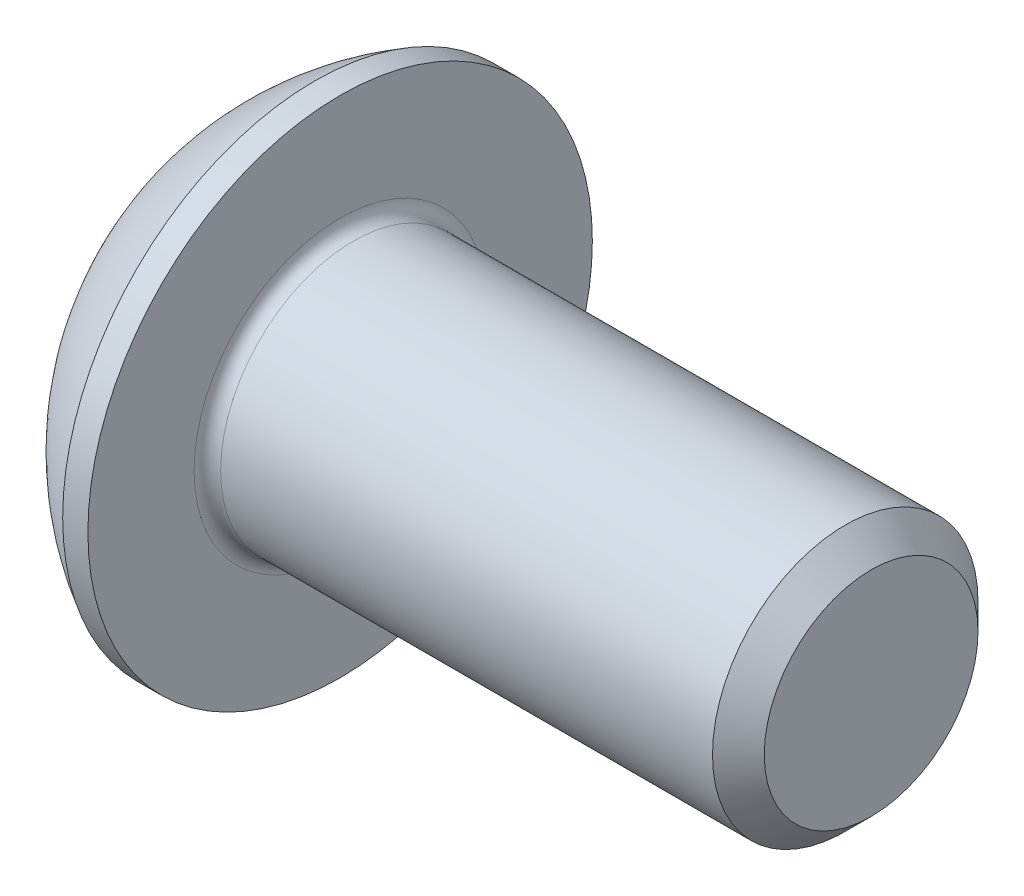
SolidWorks part; units mm, degrees
ref_plane "Plane1" through (0, 0, 0) normal (0, 0, 1) x (1, 0, 0)
ref_plane "Plane2" through (0, 0, 0) normal (0, 1, 0) x (1, 0, 0)
ref_plane "Plane3" through (0, 0, 0) normal (1, 0, 0) x (0, 0, -1)
sketch "BodySke" plane through (0, 0, 0) normal (0, 0, 1) x (1, 0, 0)
  line L0 (10.2, 0) -> (10.2, 1.61)
  line L1 (9.81, 2) -> (2.2, 2)
  line L2 (2.2, 2) -> (2.2, 3.8)
  line L3 (2.2, 3.8) -> (1.82, 3.8)
  line L4 (0, 0) -> (101.6, 0) construction
  line L5 (2.2, -3.8) -> (1.82, -3.8) construction
  line L6 (55.6768, -2) -> (2.2, -2) construction
  line L7 (10.2, 0) -> (0, 0)
  line L8 (0, 1.9) -> (0, -1.9) construction
  line L9 (0, 0) -> (0, 1.9)
  line L10 (10.2, 1.61) -> (9.81, 2)
  line L11 (10.2, -1.61) -> (9.81, -2) construction
  line L12 (2.9, 9.525) -> (2.9, -2) construction
  line L13 (2.2, 9.525) -> (2.2, -2) construction
  arc A1 (0, 1.9) -> (1.82, 3.8) centre (3.8853, 0) cw
  dimension "Diameter" = 4
  dimension "Length" = 8
  dimension "Head_dia" = 7.6
  dimension "D1" = 3.8
  dimension "Head_ht" = 2.2
  dimension "Head_side_ht" = 0.38
  dimension "Minor_dia" = 3.22
  dimension "Body_ch_ang" = 45
  dimension "Advance" = 0.7
  dimension "Thread_nom" = 8
revolve "BaseBody" add sketch "BodySke" angle 360 about L4
cosmetic thread "ThreadCosmetic" [suppressed] parameters "Thread_length"=6.6, "Thread_minor"=3.22
fillet "Fillet1" radius 0.2 1 edges at (2.2, 0, 2)
sketch "Sketch2" plane through (0, 0, 0) normal (0, 0, 1) x (1, 0, 0)
  line L0 (0, 1.25) -> (1.3, 1.25)
  line L1 (1.3, 1.25) -> (2.0217, 0)
  line L3 (2.0217, 0) -> (0, 0)
  line L4 (0, 0) -> (0, 1.25)
  line L5 (0, -1.25) -> (1.3, -1.25) construction
  line L6 (0, 0) -> (47.625, 0) construction
  dimension "D2" = 60
  dimension "PreBroach_depth" = 1.3
  dimension "PreBroach_dia" = 2.5
revolve "PreBroach" cut sketch "Sketch2" angle 360 about L6
sketch "Sketch3" plane through (0, 0, 0) normal (1, 0, 0) x (0, 0, -1)
  line L0 (-1.25, -0.7217) -> (-1.25, 0.7217)
  line L1 (-1.25, 0.7217) -> (0, 1.4434)
  line L2 (0, 1.4434) -> (1.25, 0.7217)
  line L3 (1.25, 0.7217) -> (1.25, -0.7217)
  line L4 (1.25, -0.7217) -> (0, -1.4434)
  line L5 (0, -1.4434) -> (-1.25, -0.7217)
  dimension "Hex_size" = 2.5
  dimension "D3" = 2.5
  dimension "D1" = 1.25
  dimension "D2" = 1.25
extrude "Hex" cut sketch "Sketch3" along normal blind 1.3
sketch "ThdSchSke" plane through (0, 0, 0) normal (0, 0, 1) x (1, 0, 0)
  line L0 (3.6, -1.61) -> (3.3269, -2)
  line L1 (3.6, -1.61) -> (3.8731, -2)
  line L2 (3.8731, -2) -> (3.8731, -2.5)
  line L3 (-3.175, 0) -> (5.1513, 0) construction
  line L5 (3.8731, -2.5) -> (3.3269, -2.5)
  line L6 (3.3269, -2.5) -> (3.3269, -2)
  dimension "Diameter" = 4
  dimension "Thread_minor" = 3.22
  dimension "SideAngle" = 55
  dimension "VeeAngle" = 70
  dimension "Overcut" = 5
  dimension "Start" = 3.6
revolve "ThreadSchematic" [suppressed] cut sketch "ThdSchSke" angle 360 about L3
pattern_linear "ThdSchPat" [suppressed]
equation "\"D1@BodySke\" = \"Head_dia@BodySke\" * .5"
equation "\"Thread_minor@ThreadCosmetic\" = \"Minor_dia@BodySke\""
equation "\"D1@Sketch3\" = \"Hex_size@Sketch3\" / 2"
equation "\"D2@Sketch3\" = \"D1@Sketch3\""
equation "\"D3@Sketch3\" = \"Hex_size@Sketch3\""
equation "\"Thread_length@ThreadCosmetic\" = ((sgn( (\"Length@BodySke\" - \"Advance@BodySke\" * 2.0) - \"Thread_nom@BodySke\" )-1)*( (\"Length@BodySke\" - \"Advance@BodySke\" * 2.0) - \"Thread_nom@BodySke\" ))/-2+ \"Thread_nom@BodySke\""
equation "\"Thread_minor@ThdSchSke\" = \"Minor_dia@BodySke\""
equation "\"Diameter@ThdSchSke\" = \"Diameter@BodySke\""
equation "\"Overcut@ThdSchSke\" = \"Diameter@BodySke\" * 1.25"
equation "\"Start@ThdSchSke\" = \"Head_ht@BodySke\" + \"Length@BodySke\" - \"Thread_length@ThreadCosmetic\"  '---Non-countersunk---"
equation "\"Num_threads@ThdSchPat\" = int( \"Thread_length@ThreadCosmetic\" / \"Advance@BodySke\" + 0.999 )  + 1"
equation "\"Advance@ThdSchPat\" = \"Thread_length@ThreadCosmetic\" /  (\"Num_threads@ThdSchPat\" - 1) 'relax it"
equation "\"Num_threads@ThdSchPat\" = \"Num_threads@ThdSchPat\" - sgn( \"Num_threads@ThdSchPat\" - 1) '---chamfered tips only---"
